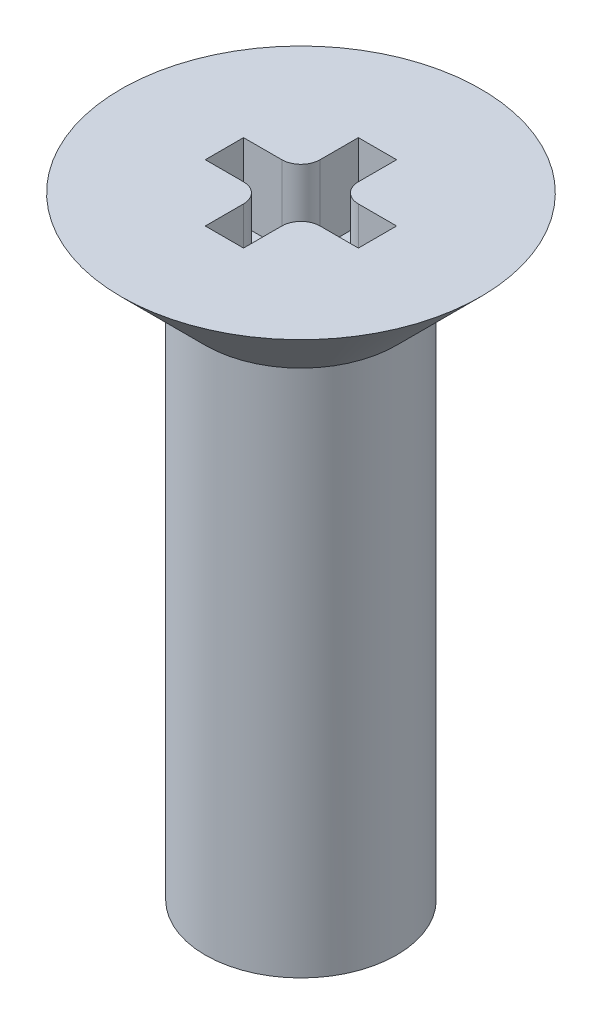
SolidWorks part; units mm, degrees
material "1023 Carbon Steel Sheet (SS)"
ref_plane "Front Plane" through (0, 0, 0) normal (0, 0, 1) x (1, 0, 0)
ref_plane "Top Plane" through (0, 0, 0) normal (0, 1, 0) x (1, 0, 0)
ref_plane "Right Plane" through (0, 0, 0) normal (1, 0, 0) x (0, 0, -1)
sketch "Sketch1" plane through (0, 0, 0) normal (1, 0, 0) x (0, 0, -1)
  line L0 (-2.35, 0) -> (2.35, 0) construction
  line L1 (-2.35, 0) -> (-1.25, -1.1) construction
  line L2 (-1.25, -1.1) -> (1.25, -1.1) construction
  line L3 (1.25, -1.1) -> (2.35, 0) construction
  line L4 (-1.25, -1.1) -> (-1.25, -1.5) construction
  line L5 (1.25, -1.1) -> (1.25, -1.5) construction
  line L6 (1.25, -1.5) -> (-1.25, -1.5) construction
  line L7 (0, 0.8723) -> (0, -0.1883) construction
  line L8 (0, 0) -> (-2.35, 0)
  line L9 (-2.35, 0) -> (-1.25, -1.1)
  line L10 (-1.25, -1.1) -> (-1.25, -1.5)
  line L11 (-1.25, -1.5) -> (0, -1.5)
  line L12 (0, 0) -> (0, -1.5)
  point P3 (0, -1.1)
  dimension "D1" = 4.7
  dimension "D2" = 90
  dimension "D3" = 2.5
  dimension "D4" = 1.5
revolve "Revolve1" add sketch "Sketch1" angle 360 about L7
sketch "Sketch2" plane through (0, -1.5, 0) normal (0, -1, 0) x (1, 0, 0)
  circle A0 centre (0, 0) radius 1.25
  dimension "D1" = 2.5
extrude "Boss-Extrude1" add sketch "Sketch2" along normal blind 6.5
sketch "Sketch3" plane through (0, 0, 0) normal (0, 1, 0) x (1, 0, 0)
  line L1 (-1, -0.25) -> (-0.5, -0.25)
  line L2 (-1, -0.25) -> (-1, 0.25)
  line L3 (-1, 0.25) -> (-0.5, 0.25)
  line L4 (1, -0.25) -> (1, 0.25)
  line L5 (-1, -0.25) -> (1, 0.25) construction
  line L6 (-1, 0.25) -> (1, -0.25) construction
  line L7 (-0.25, -1) -> (0.25, -1)
  line L8 (-0.25, -1) -> (-0.25, -0.5)
  line L9 (-0.25, 1) -> (0.25, 1)
  line L10 (0.25, -1) -> (0.25, -0.5)
  line L11 (-0.25, -1) -> (0.25, 1) construction
  line L12 (-0.25, 1) -> (0.25, -1) construction
  line L13 (-0.25, 0.5) -> (-0.25, 1)
  line L14 (0.5, 0.25) -> (1, 0.25)
  line L15 (0.25, 0.5) -> (0.25, 1)
  line L17 (0.5, -0.25) -> (1, -0.25)
  arc A0 (-0.5, 0.25) -> (-0.25, 0.5) centre (-0.5, 0.5) ccw
  arc A1 (0.25, 0.5) -> (0.5, 0.25) centre (0.5, 0.5) ccw
  arc A2 (0.5, -0.25) -> (0.25, -0.5) centre (0.5, -0.5) ccw
  arc A3 (-0.25, -0.5) -> (-0.5, -0.25) centre (-0.5, -0.5) ccw
  point P0 (0, 0)
  point P6 (0, 0)
  point P14 (-0.25, 0.25)
  point P19 (0.25, 0.25)
  point P23 (0.25, -0.25)
  dimension "D5" = 0.25
  dimension "D1" = 0.5
  dimension "D2" = 2
  dimension "D3" = 0.5
  dimension "D4" = 2
extrude "Cut-Extrude1" cut sketch "Sketch3" against normal blind 1
